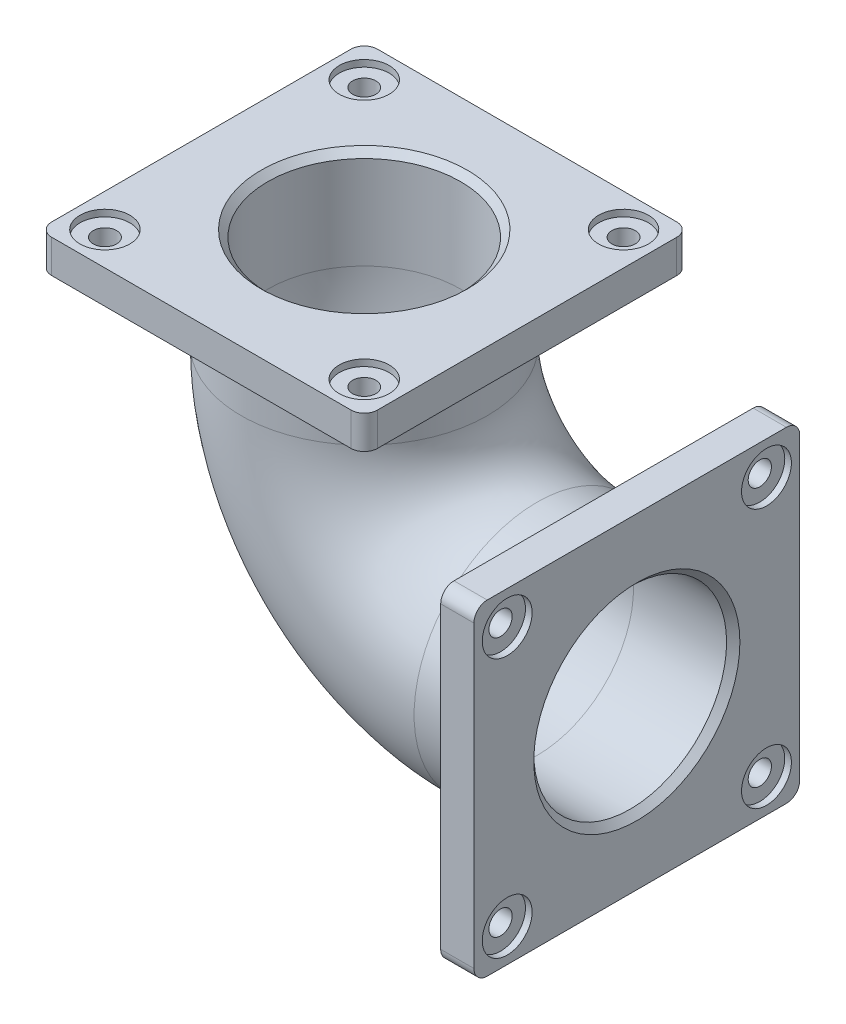
SolidWorks part; units mm, degrees
ref_plane "Front Plane" through (0, 0, 0) normal (0, 0, 1) x (1, 0, 0)
ref_plane "Top Plane" through (0, 0, 0) normal (0, 1, 0) x (1, 0, 0)
ref_plane "Right Plane" through (0, 0, 0) normal (1, 0, 0) x (0, 0, -1)
sketch "Sketch13" plane through (0, 0, 0) normal (0, 0, 1) x (1, 0, 0)
  line L0 (0, 0) -> (-150, 0)
  line L1 (-410, 260) -> (-410, 410)
  arc A0 (-150, 0) -> (-410, 260) centre (-150, 260) cw
  dimension "D2" = 260
  dimension "D1" = 150
sketch "Sketch14" plane through (0, 0, 0) normal (1, 0, 0) x (0, 0, -1)
  circle A0 centre (0, 0) radius 145
  dimension "D1" = 290
sweep "Sweep-Thin1" add profiles "Sketch14" path "Sketch13" parameters "D1"=40
sketch "Sketch16" plane through (0, 0, 0) normal (1, 0, 0) x (0, 0, -1)
  line L1 (-245, 245) -> (245, 245)
  line L2 (-245, 245) -> (-245, -245)
  line L3 (-245, -245) -> (245, -245)
  line L4 (245, 245) -> (245, -245)
  line L5 (-245, 245) -> (245, -245) construction
  line L6 (-245, -245) -> (245, 245) construction
  point P0 (0, 0)
  dimension "D1" = 490
  dimension "D2" = 490
extrude "Boss-Extrude1" add sketch "Sketch16" against normal blind 50 contours L4 L1 L2 L3
fillet "Fillet2" radius 20 4 edges at (-25, -245, 245) (-25, -245, -245) (-25, 245, -245) (-25, 245, 245)
sketch "Sketch19" plane through (0, 410, 0) normal (0, 1, 0) x (1, 0, 0)
  line L1 (-635, 245) -> (-185, 245)
  line L2 (-655, 225) -> (-655, -225)
  line L3 (-635, -245) -> (-185, -245)
  line L4 (-165, 225) -> (-165, -225)
  line L5 (-655, 245) -> (-165, -245) construction
  line L6 (-655, -245) -> (-165, 245) construction
  arc A0 (-185, 245) -> (-165, 225) centre (-185, 225) cw
  arc A1 (-655, -225) -> (-635, -245) centre (-635, -225) ccw
  arc A2 (-635, 245) -> (-655, 225) centre (-635, 225) ccw
  arc A3 (-185, -245) -> (-165, -225) centre (-185, -225) ccw
  point P0 (-410, 0)
  circle M4 centre (-410, 0) radius 185
  dimension "D3" = 20
  dimension "D1" = 490
  dimension "D2" = 490
extrude "Boss-Extrude2" add sketch "Sketch19" against normal blind 50 contours L3 A3 L4 A0 L1 A2 L2 A1 M4
sketch "Sketch20" plane through (0, 410, 0) normal (0, 1, 0) x (1, 0, 0)
  line L0 (-410, 0) -> (-150, 0) construction
  line L1 (-605, 195) -> (-215, 195) construction
  line L2 (-605, 195) -> (-605, -195) construction
  line L3 (-605, -195) -> (-215, -195) construction
  line L4 (-215, 195) -> (-215, -195) construction
  line L5 (-605, 195) -> (-215, -195) construction
  line L6 (-605, -195) -> (-215, 195) construction
  circle A0 centre (-605, 195) radius 37.5
  point P0 (-410, 0)
  dimension "D1" = 75
  dimension "D2" = 390
  dimension "D3" = 390
extrude "Cut-Extrude1" cut sketch "Sketch20" against normal blind 10
sketch "Sketch26" plane through (0, 400, 0) normal (0, 1, 0) x (1, 0, 0)
  circle A0 centre (-605, 195) radius 17.5
  dimension "D1" = 35
extrude "Cut-Extrude3" cut sketch "Sketch26" against normal up to next (40 mm away)
pattern_circular "CirPattern1" count 4 over 360 about axis through (-410, 0, 0) along (0, 1, 0) of "Cut-Extrude3", "Cut-Extrude1"
sketch "Sketch28" plane through (0, 0, 0) normal (1, 0, 0) x (0, 0, -1)
  line L1 (195, -195) -> (-195, -195) construction
  line L2 (195, -195) -> (195, 195) construction
  line L3 (195, 195) -> (-195, 195) construction
  line L4 (-195, -195) -> (-195, 195) construction
  line L5 (195, -195) -> (-195, 195) construction
  line L6 (195, 195) -> (-195, -195) construction
  circle A0 centre (-195, 195) radius 37.5
  point P0 (0, 0)
  dimension "D3" = 75
  dimension "D1" = 390
  dimension "D2" = 390
extrude "Cut-Extrude4" cut sketch "Sketch28" against normal blind 10
sketch "Sketch30" plane through (-10, 0, 0) normal (1, 0, 0) x (0, 0, -1)
  circle A0 centre (-195, 195) radius 17.5
  dimension "D1" = 35
extrude "Cut-Extrude5" cut sketch "Sketch30" against normal up to next (40 mm away)
pattern_circular "CirPattern3" count 4 over 360 about axis through (0, 0, 0) along (1, 0, 0) of "Cut-Extrude5", "Cut-Extrude4"
chamfer "Chamfer1" distance 10 angle 45 1 edges at (0, 0, -145)
chamfer "Chamfer2" distance 10 angle 45 1 edges at (-410, 410, -145)
